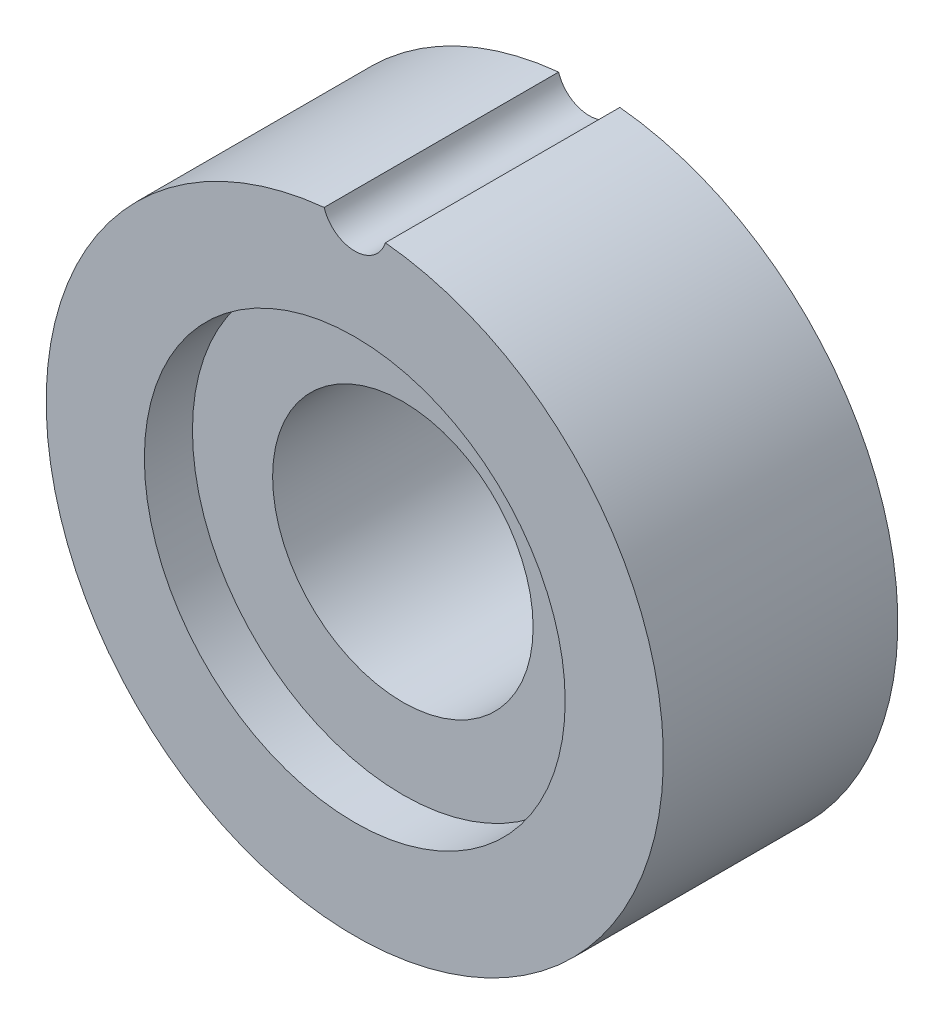
SolidWorks part; units mm, degrees
material "ABS PC"
ref_plane "Front Plane" through (0, 0, 0) normal (0, 0, 1) x (1, 0, 0)
ref_plane "Top Plane" through (0, 0, 0) normal (0, 1, 0) x (1, 0, 0)
ref_plane "Right Plane" through (0, 0, 0) normal (1, 0, 0) x (0, 0, -1)
sketch "Sketch1" plane through (0, 0, 0) normal (0, 0, 1) x (1, 0, 0)
  circle A0 centre (0, 0) radius 7.7
  circle A1 centre (0, 0) radius 3.25
  dimension "D1" = 15.4
  dimension "D2" = 6.5
extrude "Boss-Extrude1" add sketch "Sketch1" along normal blind 5.85
sketch "Sketch2" plane through (0, 0, 5.85) normal (0, 0, 1) x (1, 0, 0)
  circle A0 centre (0, 0) radius 5.25
extrude "Cut-Extrude1" cut sketch "Sketch2" against normal blind 1.2
sketch "Sketch3" plane through (0, 0, 0) normal (0, 0, -1) x (-1, 0, 0)
  circle A0 centre (0, 7.9) radius 0.8
  dimension "D1" = 7.9
extrude "Cut-Extrude2" cut sketch "Sketch3" against normal blind 10
